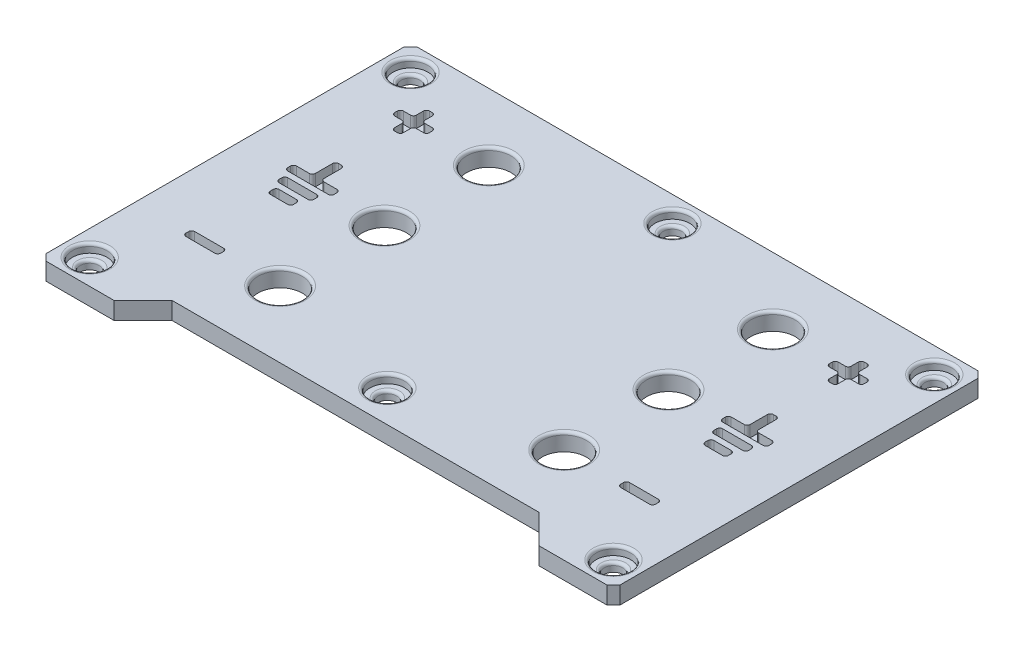
SolidWorks part; units mm, degrees
ref_plane "Front Plane" through (0, 0, 0) normal (0, 0, 1) x (1, 0, 0)
ref_plane "Top Plane" through (0, 0, 0) normal (0, 1, 0) x (1, 0, 0)
ref_plane "Right Plane" through (0, 0, 0) normal (1, 0, 0) x (0, 0, -1)
sketch "Sketch3" plane through (0, 0, 0) normal (0, 1, 0) x (1, 0, 0)
  line L0 (17.3523, -19.0435) -> (29.1096, -19.0435)
  line L5 (29.1096, -19.0435) -> (30.231, -17.9222)
  line L6 (30.231, -17.9222) -> (30.231, 43.8352)
  line L7 (30.231, 43.8352) -> (29.1096, 44.9565)
  line L8 (29.1096, 44.9565) -> (-67.6477, 44.9565)
  line L9 (-67.6477, 44.9565) -> (-68.769, 43.8352)
  line L10 (-68.769, 43.8352) -> (-68.769, -17.9222)
  line L11 (-68.769, -17.9222) -> (-67.6477, -19.0435)
  line L12 (-67.6477, -19.0435) -> (-55.8904, -19.0435)
  line L13 (-55.8904, -19.0435) -> (-50.8904, -14.0435)
  line L14 (-50.8904, -14.0435) -> (12.3523, -14.0435)
  line L15 (12.3523, -14.0435) -> (17.3523, -19.0435)
  line L16 (-19.269, 44.9565) -> (-19.269, -14.0435) construction
  line L17 (-68.769, 15.4565) -> (30.231, 15.4565) construction
  line L18 (-43.769, 44.9565) -> (-43.769, -14.0435) construction
  circle A0 centre (-64.439, 40.6265) radius 1.6
  circle A1 centre (-64.439, -14.7135) radius 1.6
  circle A2 centre (25.901, 40.6265) radius 1.6
  circle A3 centre (25.901, -14.7135) radius 1.6
  circle A4 centre (-43.769, 33.4565) radius 3.825
  circle A5 centre (-43.769, 15.4565) radius 3.825
  circle A6 centre (-43.769, -2.5435) radius 3.825
  circle A7 centre (5.231, -2.5435) radius 3.825
  circle A8 centre (5.231, 15.4565) radius 3.825
  circle A9 centre (5.231, 33.4565) radius 3.825
  circle A10 centre (-19.269, 40.6265) radius 1.6
  circle A11 centre (-19.269, -8.5435) radius 1.6
  point P22 (-19.269, 15.4565)
  point P26 (-19.269, 15.4565)
  point P28 (-43.769, 15.4565)
  point P46 (-19.269, 40.6265)
  point P47 (-19.269, -8.5435)
  dimension "D1" = 3.2
  dimension "D4" = 3.2
  dimension "D7" = 3.2
  dimension "D8" = 3.2
  dimension "D13" = 7.65
  dimension "D14" = 7.65
  dimension "D15" = 7.65
  dimension "D19" = 3.2
  dimension "D20" = 3.2
  dimension "D2" = 4.33
  dimension "D3" = 4.33
  dimension "D5" = 4.33
  dimension "D6" = 4.33
  dimension "D9" = 4.33
  dimension "D10" = 4.33
  dimension "D11" = 4.33
  dimension "D12" = 4.33
  dimension "D16" = 25
  dimension "D17" = 18
  dimension "D18" = 18
  dimension "D21" = 4.33
  dimension "D22" = 5.5
extrude "Boss-Extrude1" add sketch "Sketch3" against normal blind 3
sketch "Sketch4" plane through (0, 0, 0) normal (0, 1, 0) x (1, 0, 0)
  circle A0 centre (-64.439, 40.6265) radius 3
  circle A1 centre (-64.439, -14.7135) radius 3
  circle A2 centre (25.901, 40.6265) radius 3
  circle A3 centre (25.901, -14.7135) radius 3
  circle A4 centre (-19.269, 40.6265) radius 3
  circle A5 centre (-19.269, -8.5435) radius 3
  dimension "D1" = 6
  dimension "D2" = 6
  dimension "D3" = 6
  dimension "D4" = 6
  dimension "D5" = 6
  dimension "D6" = 6
extrude "Cut-Extrude1" cut sketch "Sketch4" against normal blind 1.5
fillet "Fillet1" radius 0.5 18 edges at (-64.439, -1.5, 16.3135) (-64.439, 0, 17.7135) (25.901, 0, 17.7135) (25.901, -1.5, 16.3135) (25.901, -1.5, -39.0265) (25.901, 0, -37.6265) (-64.439, -1.5, -39.0265) (-64.439, 0, -37.6265) (-19.269, -1.5, 10.1435) (-19.269, 0, 11.5435) (-19.269, -1.5, -39.0265) (-19.269, 0, -37.6265) (5.231, 0, -37.2815) (5.231, 0, -19.2815) (5.231, 0, -1.2815) (-43.769, 0, 6.3685) (-43.769, 0, -11.6315) (-43.769, 0, -29.6315)
sketch "Sketch5" plane through (0, 0, 0) normal (0, 1, 0) x (1, 0, 0)
  line L0 (-43.769, 33.4565) -> (-56.769, 33.4565) construction
  line L1 (-57.519, 30.4565) -> (-56.019, 30.4565)
  line L2 (-57.519, 30.4565) -> (-57.519, 32.7065)
  line L3 (-57.519, 36.4565) -> (-56.019, 36.4565)
  line L4 (-56.019, 30.4565) -> (-56.019, 32.7065)
  line L5 (-57.519, 30.4565) -> (-56.019, 36.4565) construction
  line L6 (-57.519, 36.4565) -> (-56.019, 30.4565) construction
  line L7 (-59.769, 32.7065) -> (-57.519, 32.7065)
  line L8 (-59.769, 32.7065) -> (-59.769, 34.2065)
  line L9 (-59.769, 34.2065) -> (-57.519, 34.2065)
  line L10 (-53.769, 32.7065) -> (-53.769, 34.2065)
  line L11 (-59.769, 32.7065) -> (-53.769, 34.2065) construction
  line L12 (-59.769, 34.2065) -> (-53.769, 32.7065) construction
  line L13 (-56.019, 34.2065) -> (-53.769, 34.2065)
  line L14 (-57.519, 34.2065) -> (-57.519, 36.4565)
  line L15 (-56.019, 32.7065) -> (-53.769, 32.7065)
  line L16 (-56.769, 33.4565) -> (-56.769, -2.5435) construction
  line L17 (-56.019, 34.2065) -> (-56.019, 36.4565)
  line L18 (-56.019, 16.7709) -> (-52.769, 16.7709)
  line L19 (-59.769, -3.2935) -> (-53.769, -3.2935)
  line L20 (-59.769, -3.2935) -> (-59.769, -1.7935)
  line L21 (-59.769, -1.7935) -> (-53.769, -1.7935)
  line L22 (-53.769, -3.2935) -> (-53.769, -1.7935)
  line L23 (-59.769, -3.2935) -> (-53.769, -1.7935) construction
  line L24 (-59.769, -1.7935) -> (-53.769, -3.2935) construction
  line L26 (-57.519, 16.7709) -> (-57.519, 20.7709)
  line L27 (-57.519, 20.7709) -> (-56.019, 20.7709)
  line L28 (-56.019, 16.7709) -> (-56.019, 20.7709)
  line L29 (-57.519, 16.7709) -> (-56.019, 20.7709) construction
  line L30 (-57.519, 20.7709) -> (-56.019, 16.7709) construction
  line L31 (-52.769, 16.7709) -> (-52.769, 15.2709)
  line L32 (-52.769, 15.2709) -> (-60.769, 15.2709)
  line L33 (-60.769, 15.2709) -> (-60.769, 16.7709)
  line L34 (-60.769, 16.7709) -> (-57.519, 16.7709)
  line L36 (-59.769, 12.7709) -> (-53.769, 12.7709)
  line L37 (-59.769, 12.7709) -> (-59.769, 14.2709)
  line L38 (-59.769, 14.2709) -> (-53.769, 14.2709)
  line L39 (-53.769, 12.7709) -> (-53.769, 14.2709)
  line L40 (-59.769, 12.7709) -> (-53.769, 14.2709) construction
  line L41 (-59.769, 14.2709) -> (-53.769, 12.7709) construction
  line L42 (-58.769, 10.2709) -> (-54.769, 10.2709)
  line L43 (-58.769, 10.2709) -> (-58.769, 11.7709)
  line L44 (-58.769, 11.7709) -> (-54.769, 11.7709)
  line L45 (-54.769, 10.2709) -> (-54.769, 11.7709)
  line L46 (-58.769, 10.2709) -> (-54.769, 11.7709) construction
  line L47 (-58.769, 11.7709) -> (-54.769, 10.2709) construction
  point P0 (-56.769, 33.4565)
  point P5 (-56.769, 33.4565)
  point P22 (-43.769, -2.5435)
  point P23 (-56.769, 18.7709)
  point P29 (-56.769, 15.2709)
  point P35 (-56.769, 11.0209)
  point P37 (-56.769, 13.5209)
  dimension "D1" = 6
  dimension "D2" = 1.5
  dimension "D3" = 10
  dimension "D4" = 1.5
  dimension "D5" = 6
  dimension "D6" = 1.5
  dimension "D7" = 8
  dimension "D8" = 1.5
  dimension "D9" = 4
  dimension "D10" = 1.5
  dimension "D11" = 6
  dimension "D12" = 1
  dimension "D13" = 1
  dimension "D14" = 1.5
  dimension "D15" = 4
  dimension "D16" = 6
sketch "Sketch6" plane through (0, 0, 0) normal (0, 1, 0) x (1, 0, 0)
  line L0 (29.1096, 44.9565) -> (-67.6477, 44.9565) construction
  line L1 (-50.8904, -14.0435) -> (12.3523, -14.0435) construction
  point P0 (-19.269, 44.9565)
  point P1 (-19.269, -14.0435)
ref_plane "Plane1" through (-19.269, 0, 0) normal (-1, 0, 0) x (0, 0, 1)
extrude "Cut-Extrude2" cut sketch "Sketch5" against normal blind 2
mirror "Mirror1" about plane through (-19.269, 0, 0) normal (-1, 0, 0) of "Cut-Extrude2"
fillet "Fillet2" radius 0.5 64 edges at (21.231, -1, 1.7935) (15.231, -1, 1.7935) (15.231, -1, 3.2935) (21.231, -1, 3.2935) (20.231, -1, -10.2709) (16.231, -1, -10.2709) (16.231, -1, -11.7709) (20.231, -1, -11.7709) (21.231, -1, -14.2709) (15.231, -1, -14.2709) (15.231, -1, -12.7709) (21.231, -1, -12.7709) (22.231, -1, -15.2709) (14.231, -1, -15.2709) (22.231, -1, -16.7709) (18.981, -1, -16.7709) (18.981, -1, -20.7709) (14.231, -1, -16.7709) (17.481, -1, -16.7709) (17.481, -1, -20.7709) (21.231, -1, -32.7065) (18.981, -1, -32.7065) (18.981, -1, -30.4565) (17.481, -1, -30.4565) (17.481, -1, -32.7065) (15.231, -1, -32.7065) (15.231, -1, -34.2065) (17.481, -1, -36.4565) (17.481, -1, -34.2065) (18.981, -1, -36.4565) (18.981, -1, -34.2065) (21.231, -1, -34.2065) (-53.769, -1, 1.7935) (-59.769, -1, 1.7935) (-59.769, -1, 3.2935) (-53.769, -1, 3.2935) (-54.769, -1, -10.2709) (-58.769, -1, -10.2709) (-58.769, -1, -11.7709) (-54.769, -1, -11.7709) (-53.769, -1, -14.2709) (-59.769, -1, -14.2709) (-59.769, -1, -12.7709) (-53.769, -1, -12.7709) (-52.769, -1, -15.2709) (-60.769, -1, -15.2709) (-60.769, -1, -16.7709) (-52.769, -1, -16.7709) (-56.019, -1, -16.7709) (-57.519, -1, -16.7709) (-56.019, -1, -20.7709) (-57.519, -1, -20.7709) (-53.769, -1, -32.7065) (-56.019, -1, -32.7065) (-56.019, -1, -30.4565) (-57.519, -1, -30.4565) (-57.519, -1, -32.7065) (-59.769, -1, -32.7065) (-59.769, -1, -34.2065) (-57.519, -1, -34.2065) (-56.019, -1, -34.2065) (-53.769, -1, -34.2065) (-57.519, -1, -36.4565) (-56.019, -1, -36.4565)
